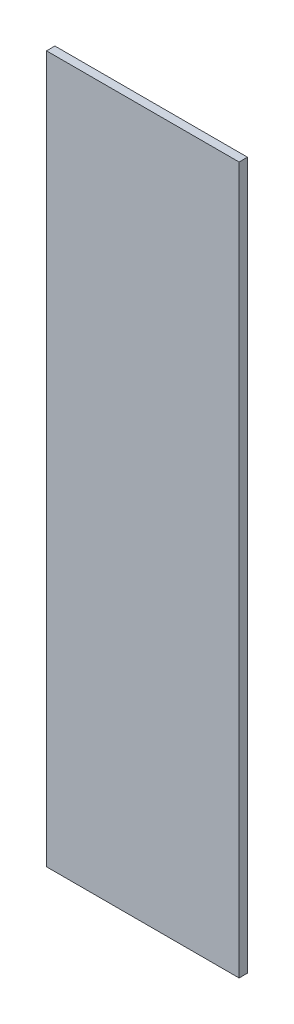
SolidWorks part; units mm, degrees
material "Acrylic (Medium-high impact)"
ref_plane "Front Plane" through (0, 0, 0) normal (0, 0, 1) x (1, 0, 0)
ref_plane "Top Plane" through (0, 0, 0) normal (0, 1, 0) x (1, 0, 0)
ref_plane "Right Plane" through (0, 0, 0) normal (1, 0, 0) x (0, 0, -1)
sketch "Sketch3" plane through (0, 0, 0) normal (0, 0, 1) x (1, 0, 0)
  line L1 (0, 0) -> (-73, 0)
  line L2 (0, 0) -> (0, 267.9)
  line L3 (0, 267.9) -> (-73, 267.9)
  line L4 (-73, 0) -> (-73, 267.9)
  dimension "D1" = 73
  dimension "D2" = 267.9
extrude "Boss-Extrude1" add sketch "Sketch3" along normal blind 3.175
